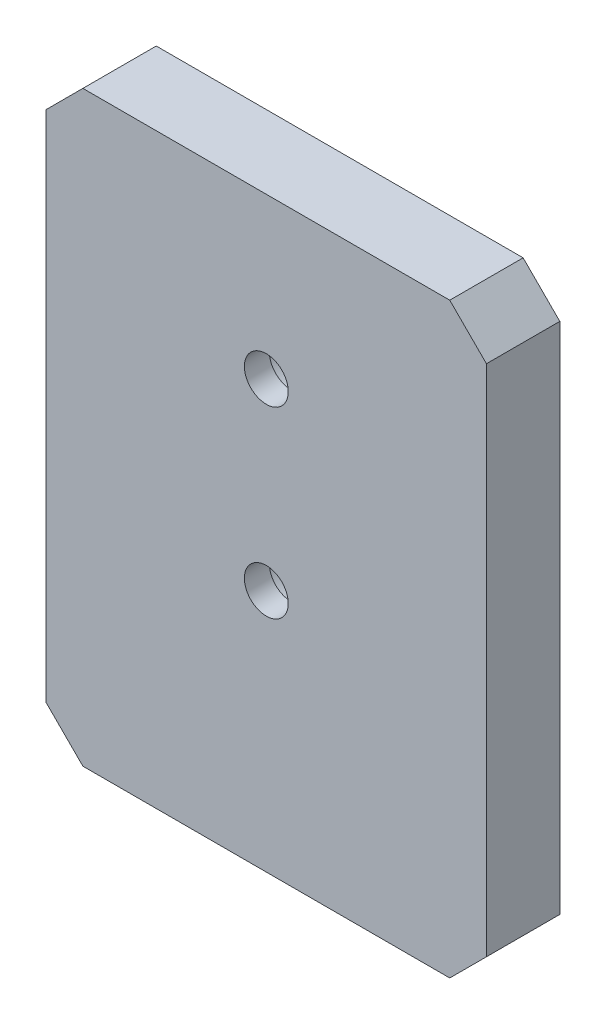
SolidWorks part; units mm, degrees
ref_plane "Front Plane" through (0, 0, 0) normal (0, 0, 1) x (1, 0, 0)
ref_plane "Top Plane" through (0, 0, 0) normal (0, 1, 0) x (1, 0, 0)
ref_plane "Right Plane" through (0, 0, 0) normal (1, 0, 0) x (0, 0, -1)
sketch "Sketch1" plane through (0, 0, 0) normal (0, 0, 1) x (1, 0, 0)
  line L1 (-19.05, -25.4) -> (19.05, -25.4)
  line L2 (-19.05, -25.4) -> (-19.05, 25.4)
  line L3 (-19.05, 25.4) -> (19.05, 25.4)
  line L4 (19.05, -25.4) -> (19.05, 25.4)
  line L5 (-19.05, -25.4) -> (19.05, 25.4) construction
  line L6 (-19.05, 25.4) -> (19.05, -25.4) construction
  point P0 (0, 0)
  dimension "D1" = 50.8
  dimension "D2" = 38.1
extrude "Boss-Extrude1" add sketch "Sketch1" against normal blind 6.35
chamfer "Chamfer1" distance 3.175 angle 45 4 edges at (-19.05, -25.4, -3.175) (19.05, -25.4, -3.175) (-19.05, 25.4, -3.175) (19.05, 25.4, -3.175)
ref_plane "Plane1" through (0, 0, 0) normal (1, 0, 0) x (0, 0, -1)
sketch "Sketch2" plane through (0, 0, -6.35) normal (0, 0, -1) x (-1, 0, 0)
  circle A0 centre (0, 11.557) radius 2.3812 construction
  circle A1 centre (0, -4.318) radius 2.3812 construction
  circle A2 centre (0, 11.557) radius 2.3812
  circle A3 centre (0, -4.318) radius 2.3812
  circle A4 centre (0, -4.318) radius 3.4928
  circle A5 centre (0, 11.557) radius 3.7834
  point P9 (0, -4.318)
  point P10 (0, 11.557)
  point P11 (0, 11.557)
hole_wizard "CBORE for #6 Socket Head Cap Screw1" positions "Sketch5" profile "Sketch6" counterbore size "#6" standard "ANSI Inch" end condition through all
sketch "Sketch5" plane through (0, 0, -6.35) normal (0, 0, -1) x (-1, 0, 0)
  point P0 (0, -4.318)
  point P3 (0, 11.557)
sketch "Sketch6" plane through (0, -4.318, -6.35) normal (1, 0, 0) x (0, 1, 0)
  line L0 (0, 0) -> (0, 6.35)
  line L1 (0, 6.35) -> (1.8986, 6.35)
  line L3 (1.8986, 6.35) -> (1.8986, 4.191)
  line L4 (1.8986, 4.191) -> (3.5725, 4.191)
  line L5 (3.5725, 4.191) -> (3.5725, 0)
  line L7 (3.5725, 0) -> (0, 0)
  line L11 (0, -6.35) -> (0, 107.95) construction
  dimension "Thru Hole Dia." = 3.7973
  dimension "Thru Hole Depth" = 6.35
  dimension "C'Bore Dia." = 7.145
  dimension "C'Bore Depth" = 4.191
